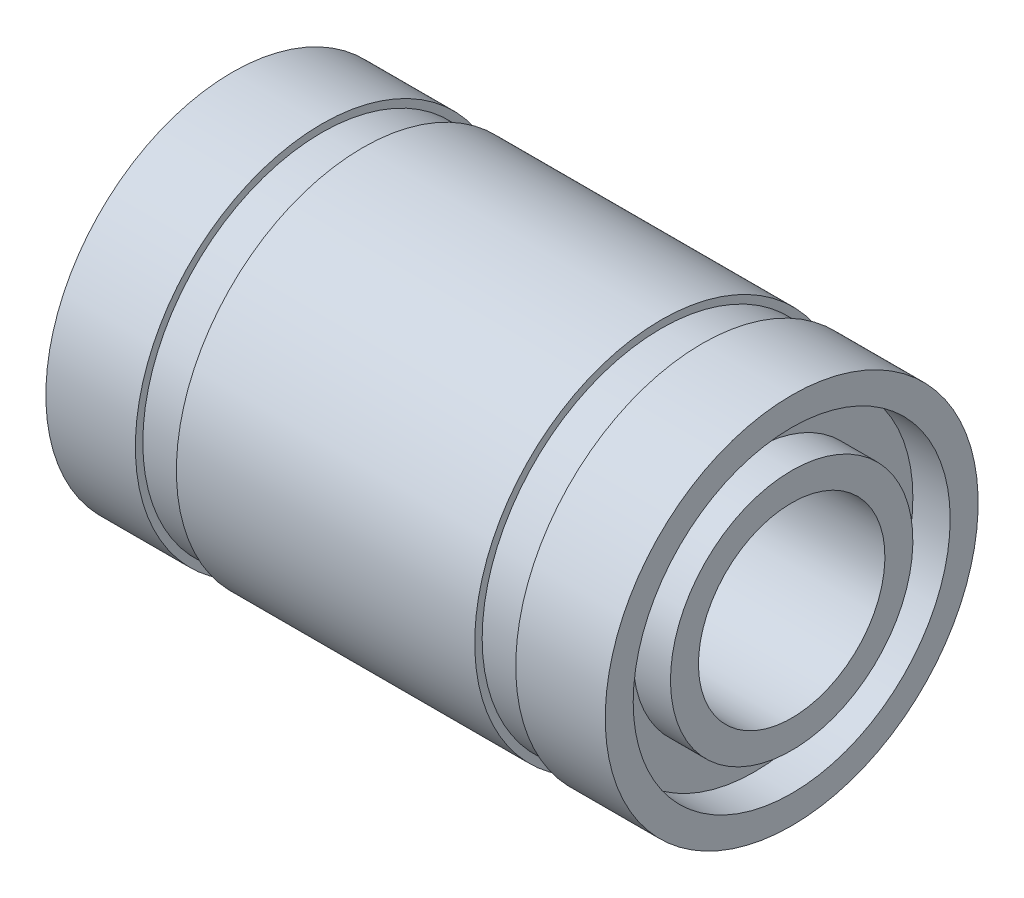
SolidWorks part; units mm, degrees
material "Ст3сп ГОСТ 535-2005"
ref_plane "Plano frontal" through (0, 0, 0) normal (0, 0, 1) x (1, 0, 0)
ref_plane "Plano superior" through (0, 0, 0) normal (0, 1, 0) x (1, 0, 0)
ref_plane "Plano direito" through (0, 0, 0) normal (1, 0, 0) x (0, 0, -1)
sketch "Esboço1" plane through (0, 0, 0) normal (0, 0, 1) x (1, 0, 0)
  line L0 (-7.5, 5) -> (-5.1, 5)
  line L1 (-5.1, 5) -> (-5.1, 4.8)
  line L2 (-5.1, 4.8) -> (-4, 4.8)
  line L3 (-4, 4.8) -> (-4, 5)
  line L4 (-4, 5) -> (4, 5)
  line L5 (4, 5) -> (4, 4.8)
  line L6 (4, 4.8) -> (5.1, 4.8)
  line L7 (5.1, 4.8) -> (5.1, 5)
  line L8 (5.1, 5) -> (7.5, 5)
  line L9 (7.5, 5) -> (7.5, 4.25)
  line L10 (7.5, 2.5) -> (-7.5, 2.5)
  line L11 (-7.5, 2.5) -> (-7.5, 3.25)
  line L12 (0, 2.5) -> (0, 0) construction
  line L13 (0, 0) -> (-86.5, 0) construction
  line L14 (-7.5, 4.25) -> (-7.5, 5)
  line L15 (-7.5, 4.25) -> (-6.5, 4.25)
  line L16 (7.5, 3.25) -> (7.5, 2.5)
  line L17 (-6.5, 4.25) -> (-6.5, 3.25)
  line L18 (-6.5, 3.25) -> (-7.5, 3.25)
  line L19 (7.5, 4.25) -> (6.5, 4.25)
  line L21 (7.5, 3.25) -> (6.5, 3.25)
  line L22 (6.5, 4.25) -> (6.5, 3.25)
  dimension "D1" = 15
  dimension "D2" = 10.2
  dimension "D3" = 1.1
  dimension "D4" = 5
  dimension "D5" = 10
  dimension "D6" = 9.6
  dimension "D7" = 1
  dimension "D8" = 1
  dimension "D9" = 1
  dimension "D10" = 1
revolve "Revolução1" add sketch "Esboço1" angle 360 about L13
